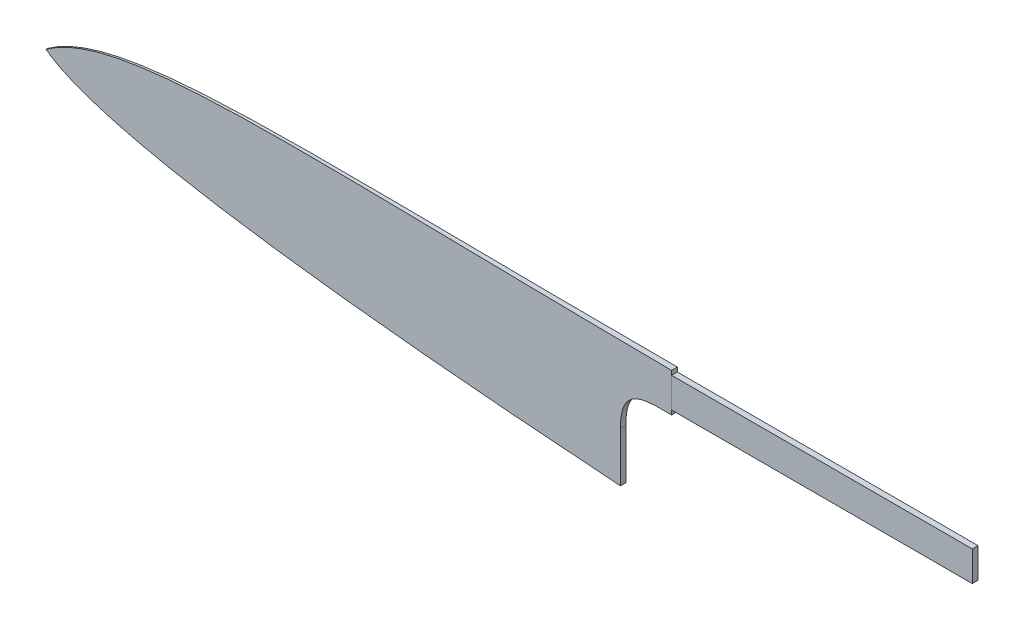
SolidWorks part; units mm, degrees
other "Caméra1"
material "1.7014 (17CrS3)"
ref_plane "Plan de face" through (0, 0, 0) normal (0, 0, 1) x (1, 0, 0)
ref_plane "Plan de dessus" through (0, 0, 0) normal (0, 1, 0) x (1, 0, 0)
ref_plane "Plan de droite" through (0, 0, 0) normal (1, 0, 0) x (0, 0, -1)
other "Centre de masse"
sketch "Esquisse1" plane through (0, 0, 0) normal (0, 0, 1) x (1, 0, 0)
  line L0 (73.5542, -46.7998) -> (343.1991, -46.7998) construction
sketch "Esquisse2" plane through (0, 0, 0) normal (0, 0, 1) x (1, 0, 0)
  line L0 (220, 48) -> (220, 46.5)
  line L1 (220, 46.5) -> (325, 46.5)
  line L2 (325, 46.5) -> (325, 36)
  line L3 (325, 36) -> (220, 36)
  line L4 (220, 36) -> (220, 34.5)
  line L5 (202, 21.363) -> (202, 4)
  spline S0 degree 2 poles (202, 4) (26.0077, 14.5313) (0, 34.3739) knots 0 0 0 1 1 1
  spline S1 degree 3 poles (0, 34.3739) (25.3246, 53.6536) (88.6496, 48) (220, 48) knots 0 0 0 0 1 1 1 1
  spline S2 degree 3 poles (220, 34.5) (204.772, 34.5) (202, 32.5657) (202, 21.363) knots 0 0 0 0 1 1 1 1
  point P5 (219.8445, 34.3739)
  point P9 (0, 0)
  point P11 (0, 0)
  point P12 (0, 0)
  point P13 (0, 0)
  point P14 (0, 0)
  point P15 (0, 0)
  point P16 (220.0226, 46.586)
  point P17 (0, 0)
  point P18 (0, 0)
  point P19 (0, 0)
  point P20 (0, 0)
  point P21 (0, 0)
  point P22 (0, 0)
  point P23 (0, 0)
  point P24 (0, 0)
  point P25 (0, 0)
  dimension "D1" = 1.5
  dimension "D2" = 105
  dimension "D3" = 10.5
  dimension "D4" = 1.5
sketch "Esquisse3" plane through (0, 0, 0) normal (0, 1, 0) x (1, 0, 0)
  line L0 (341.486, 0) -> (0, 0)
  line L1 (-9.9957, 0) -> (-9.9998, -0.4318)
  line L2 (-9.9998, -0.4318) -> (0, -0.5)
  line L3 (220, -2) -> (341.486, -2)
  line L4 (341.486, -2) -> (341.486, 0)
  line L5 (0, 0) -> (-9.9957, 0)
  line L6 (0, -0.5) -> (220, -2)
  point P3 (-14.6605, 6.5298)
  point P9 (-0.3698, -7.2209)
  point P10 (3.2029, 0)
  point P11 (0, 0)
  point P12 (0, 0)
  point P13 (0, 0)
  point P14 (0, 0)
  point P15 (88.8876, -3.2586)
  point P16 (0, 0)
  point P17 (-11.0192, -0.4754)
  point P18 (0, 0)
  point P19 (0, 0)
  point P20 (-8.1106, -2.6031)
  point P21 (0, 0)
  point P22 (0, 0)
  dimension "D1" = 220
  dimension "D2" = 2
  dimension "D3" = 0.5
extrude "Boss.-Extru.1" add sketch "Esquisse3" along normal blind 52
sketch "Esquisse4" plane through (0, 0, 2) normal (0, 0, 1) x (1, 0, 0)
  line L0 (325, 46.5) -> (325, 36)
  line L1 (325, 36) -> (220, 36)
  line L2 (220, 36) -> (220, 34.5)
  line L3 (325, 46.5) -> (220, 46.5)
  line L4 (220, 46.5) -> (220, 48)
  line L5 (202, 4) -> (202, 21.363)
  line L6 (341.486, 0) -> (-9.9998, 0)
  line L7 (-9.9998, 0) -> (-9.9998, 52)
  line L8 (-9.9998, 52) -> (341.486, 52)
  line L9 (341.486, 52) -> (341.486, 0)
  spline S0 degree 2 poles (202, 4) (25.7823, 14.7636) (0, 34.3739) knots 0 0 0 1 1 1
  spline S1 degree 3 poles (0, 34.3739) (26.7406, 53.8106) (88.506, 48) (220, 48) knots 0 0 0 0 1 1 1 1
  spline S2 degree 3 poles (220, 34.5) (210.1486, 34.5) (202, 34.9028) (202, 21.363) knots 0 0 0 0 1 1 1 1
extrude "Enlèv. mat.-Extru.1" cut sketch "Esquisse4" against normal blind 52
ref_plane "Plan1" through (202, 0, 0) normal (1, 0, 0) x (0, 0, -1)
sketch "Esquisse6" plane through (202, 0, 0) normal (1, 0, 0) x (0, 0, -1)
  line L0 (0, 4) -> (-0.6651, 7)
  line L1 (-0.6651, 7) -> (-1.8773, 20)
  line L2 (-1.8773, 21.363) -> (-1.8773, 4) construction
  line L3 (-1.8773, 20) -> (-1.8773, 4)
  line L4 (-1.8773, 4) -> (0, 4)
  line L5 (0, 34.3739) -> (0, 4) construction
  dimension "D1" = 12.5
  dimension "D2" = 16
  dimension "D3" = 3
